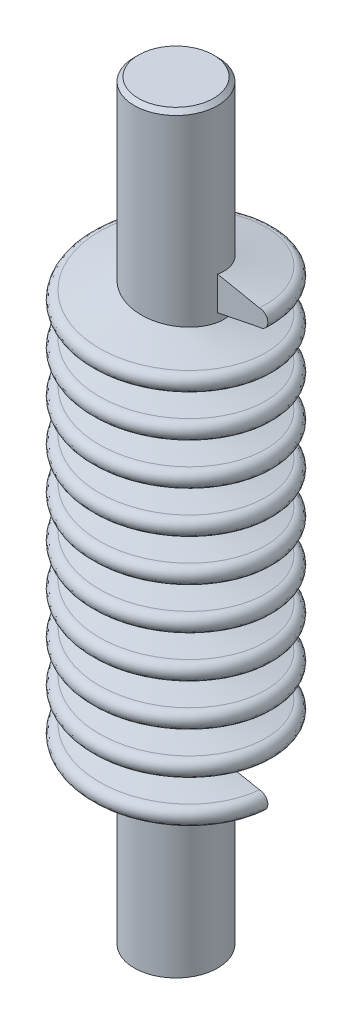
SolidWorks part; units mm, degrees
ref_plane "Front Plane" through (0, 0, 0) normal (0, 0, 1) x (1, 0, 0)
ref_plane "Top Plane" through (0, 0, 0) normal (0, 1, 0) x (1, 0, 0)
ref_plane "Right Plane" through (0, 0, 0) normal (1, 0, 0) x (0, 0, -1)
sketch "Sketch1" plane through (0, 0, 0) normal (0, 1, 0) x (1, 0, 0)
  circle A0 centre (0, 0) radius 5
  dimension "D1" = 10
extrude "Boss-Extrude2" add sketch "Sketch1" along normal blind 90
chamfer "Chamfer1" distance 0.5 angle 45 1 edges at (0, 90, 5)
ref_plane "Plane1" through (0, 70, 0) normal (0, 1, 0) x (1, 0, 0)
sketch "Sketch3" plane through (0, 70, 0) normal (0, 1, 0) x (1, 0, 0)
  circle A0 centre (0, 0) radius 5 construction
  circle A1 centre (0, 0) radius 5
curve "Helix/Spiral1" pitch 5 height 50 turns 10
sketch "Sketch4" plane through (0, 0, 0) normal (0, 0, 1) x (1, 0, 0)
  line L0 (5, 70) -> (6.3876, 70) construction
  line L1 (4.95, 70) -> (-4.95, 70) construction
  line L2 (5, 0) -> (5, 89.5) construction
  line L3 (4.781, 72) -> (5, 72)
  line L4 (4.781, 72) -> (4.781, 68)
  line L5 (4.781, 68) -> (5, 68)
  line L7 (5, 72) -> (10, 71)
  line L8 (5, 68) -> (10, 69)
  line L9 (0, 100.8871) -> (0, -7.1777) construction
  arc A0 (10, 69) -> (10, 71) centre (10, 70) ccw
  spline S0 degree 3 poles (5, 70) (5, 69.8965) (4.7397, 69.6872) (3.6276, 69.3751) (1.9632, 69.0625) (0, 68.75) (-1.9632, 68.4375) (-3.6276, 68.125) (-4.7397, 67.8125) (-5.1302, 67.5) (-4.7397, 67.1875) (-3.6276, 66.875) (-1.4084, 66.4583) (1.4084, 66.0417) (3.6276, 65.625) (4.7397, 65.3125) (5.1302, 65) (4.7397, 64.6875) (3.6276, 64.375) (1.4084, 63.9583) (-1.4084, 63.5417) (-3.6276, 63.125) (-4.7397, 62.8125) (-5.1302, 62.5) (-4.7397, 62.1875) (-3.6276, 61.875) (-1.4084, 61.4583) (1.4084, 61.0417) (3.6276, 60.625) (4.7397, 60.3125) (5.1302, 60) (4.7397, 59.6875) (3.6276, 59.375) (1.4084, 58.9583) (-1.4084, 58.5417) (-3.6276, 58.125) (-4.7397, 57.8125) (-5.1302, 57.5) (-4.7397, 57.1875) (-3.6276, 56.875) (-1.4084, 56.4583) (1.4084, 56.0417) (3.6276, 55.625) (4.7397, 55.3125) (5.1302, 55) (4.7397, 54.6875) (3.6276, 54.375) (1.4084, 53.9583) (-1.4084, 53.5417) (-3.6276, 53.125) (-4.7397, 52.8125) (-5.1302, 52.5) (-4.7397, 52.1875) (-3.6276, 51.875) (-1.4084, 51.4583) (1.4084, 51.0417) (3.6276, 50.625) (4.7397, 50.3125) (5.1302, 50) (4.7397, 49.6875) (3.6276, 49.375) (1.4084, 48.9583) (-1.4084, 48.5417) (-3.6276, 48.125) (-4.7397, 47.8125) (-5.1302, 47.5) (-4.7397, 47.1875) (-3.6276, 46.875) (-1.4084, 46.4583) (1.4084, 46.0417) (3.6276, 45.625) (4.7397, 45.3125) (5.1302, 45) (4.7397, 44.6875) (3.6276, 44.375) (1.4084, 43.9583) (-1.4084, 43.5417) (-3.6276, 43.125) (-4.7397, 42.8125) (-5.1302, 42.5) (-4.7397, 42.1875) (-3.6276, 41.875) (-1.4084, 41.4583) (1.4084, 41.0417) (3.6276, 40.625) (4.7397, 40.3125) (5.1302, 40) (4.7397, 39.6875) (3.6276, 39.375) (1.4084, 38.9583) (-1.4084, 38.5417) (-3.6276, 38.125) (-4.7397, 37.8125) (-5.1302, 37.5) (-4.7397, 37.1875) (-3.6276, 36.875) (-1.4084, 36.4583) (1.4084, 36.0417) (3.6276, 35.625) (4.7397, 35.3125) (5.1302, 35) (4.7397, 34.6875) (3.6276, 34.375) (1.4084, 33.9583) (-1.4084, 33.5417) (-3.6276, 33.125) (-4.7397, 32.8125) (-5.1302, 32.5) (-4.7397, 32.1875) (-3.6276, 31.875) (-1.4084, 31.4583) (1.4084, 31.0417) (3.6276, 30.625) (4.7397, 30.3125) (5.1302, 30) (4.7397, 29.6875) (3.6276, 29.375) (1.4084, 28.9583) (-1.4084, 28.5417) (-3.6276, 28.125) (-4.7397, 27.8125) (-5.1302, 27.5) (-4.7397, 27.1875) (-3.6276, 26.875) (-1.4084, 26.4583) (1.4084, 26.0417) (3.6276, 25.625) (4.7397, 25.3125) (5.1302, 25) (4.7397, 24.6875) (3.6276, 24.375) (1.4084, 23.9583) (-1.4084, 23.5417) (-3.6276, 23.125) (-4.7397, 22.8125) (-5.1302, 22.5) (-4.7397, 22.1875) (-3.6276, 21.875) (-1.9632, 21.5625) (0, 21.25) (1.9632, 20.9375) (3.6276, 20.6249) (4.7397, 20.3128) (5, 20.1035) (5, 20) knots 0 0 0 0 0.00625 0.0125 0.01875 0.025 0.03125 0.0375 0.04375 0.05 0.05625 0.0625 0.06875 0.08125 0.0875 0.09375 0.1 0.10625 0.1125 0.11875 0.13125 0.1375 0.14375 0.15 0.15625 0.1625 0.16875 0.18125 0.1875 0.19375 0.2 0.20625 0.2125 0.21875 0.23125 0.2375 0.24375 0.25 0.25625 0.2625 0.26875 0.28125 0.2875 0.29375 0.3 0.30625 0.3125 0.31875 0.33125 0.3375 0.34375 0.35 0.35625 0.3625 0.36875 0.38125 0.3875 0.39375 0.4 0.40625 0.4125 0.41875 0.43125 0.4375 0.44375 0.45 0.45625 0.4625 0.46875 0.48125 0.4875 0.49375 0.5 0.50625 0.5125 0.51875 0.53125 0.5375 0.54375 0.55 0.55625 0.5625 0.56875 0.58125 0.5875 0.59375 0.6 0.60625 0.6125 0.61875 0.63125 0.6375 0.64375 0.65 0.65625 0.6625 0.66875 0.68125 0.6875 0.69375 0.7 0.70625 0.7125 0.71875 0.73125 0.7375 0.74375 0.75 0.75625 0.7625 0.76875 0.78125 0.7875 0.79375 0.8 0.80625 0.8125 0.81875 0.83125 0.8375 0.84375 0.85 0.85625 0.8625 0.86875 0.88125 0.8875 0.89375 0.9 0.90625 0.9125 0.91875 0.93125 0.9375 0.94375 0.95 0.95625 0.9625 0.96875 0.975 0.98125 0.9875 0.99375 1 1 1 1 construction
  dimension "1" = 1
  dimension "D1" = 4
  dimension "D2" = 2
  dimension "D3" = 5
sweep "Sweep1" add profiles "Sketch4" path "Helix/Spiral1"
